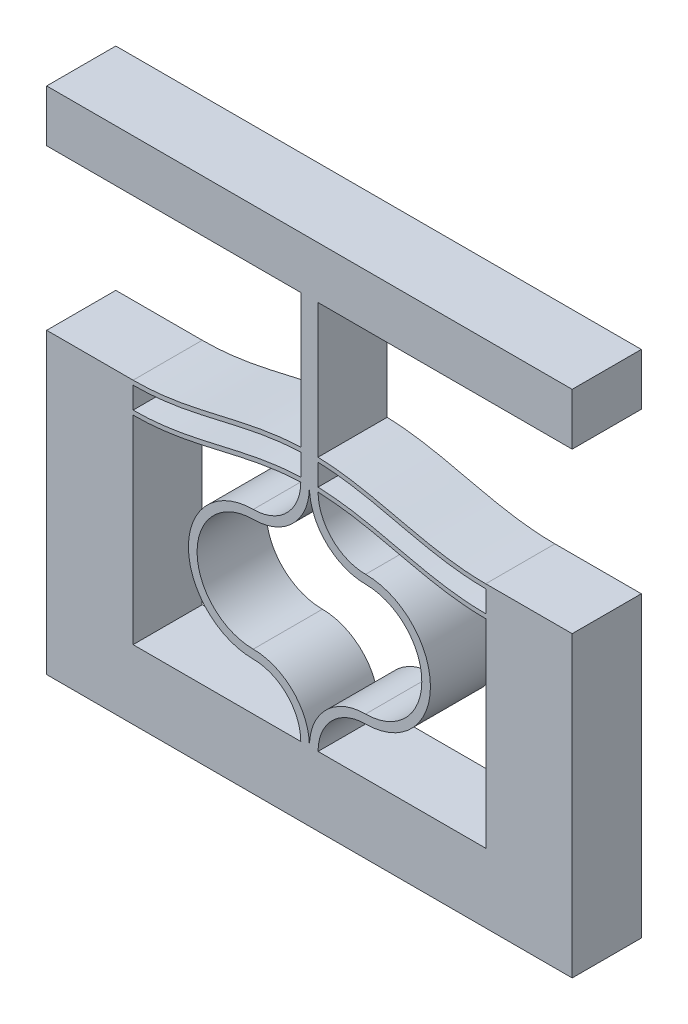
SolidWorks part; units mm, degrees
ref_plane "Front Plane" through (0, 0, 0) normal (0, 0, 1) x (1, 0, 0)
ref_plane "Top Plane" through (0, 0, 0) normal (0, 1, 0) x (1, 0, 0)
ref_plane "Right Plane" through (0, 0, 0) normal (1, 0, 0) x (0, 0, -1)
sketch "Sketch1" plane through (0, 0, 0) normal (0, 0, 1) x (1, 0, 0)
  line L4 (0, 11.5) -> (0, 0)
  line L5 (10.2, 0) -> (10.2, 13) construction
  line L6 (10.2, 13) -> (10.2, 15.9911) construction
  line L17 (9.7, 0) -> (0, 0)
  line L18 (10.7, 0) -> (20.4, 0)
  line L19 (20.4, 0) -> (20.4, 11.5)
  line L20 (10.7, 13.2411) -> (10.7, 14.4911)
  line L21 (9.7, 13.2411) -> (9.7, 14.4911)
  line L22 (10.7, 14.7411) -> (10.7, 15.9911)
  line L23 (10.7, 15.9911) -> (9.7, 15.9911)
  line L24 (9.7, 15.9911) -> (9.7, 14.7411)
  line L31 (-5, 13.25) -> (-5, -4)
  line L32 (-5, -4) -> (25.4, -4)
  line L33 (25.4, -4) -> (25.4, 13.25)
  line L34 (0, 11.75) -> (0, 13)
  line L36 (-5, 13.25) -> (0, 13.25)
  line L37 (25.4, 13.25) -> (20.4, 13.25)
  line L38 (20.4, 11.75) -> (20.4, 13)
  arc A0 (10.2, 13) -> (6.95, 9.75) centre (6.95, 13) cw
  arc A1 (6.95, 9.75) -> (6.95, 3.25) centre (6.95, 6.5) ccw
  arc A2 (6.95, 3.25) -> (10.2, 0) centre (6.95, 0) cw
  arc A3 (9.7, 12.9911) -> (6.95, 10.25) centre (6.95, 13) cw
  arc A4 (6.95, 10.25) -> (6.95, 2.75) centre (6.95, 6.5) ccw
  arc A5 (6.95, 2.75) -> (9.7, 0) centre (6.95, 0) cw
  arc A6 (9.7, 13) -> (6.95, 10.25) centre (6.95, 13) cw construction
  arc A7 (13.45, 3.25) -> (10.2, 0) centre (13.45, 0) ccw
  arc A8 (13.45, 2.75) -> (10.7, 0) centre (13.45, 0) ccw
  arc A9 (13.45, 9.75) -> (13.45, 3.25) centre (13.45, 6.5) cw
  arc A10 (13.45, 10.25) -> (13.45, 2.75) centre (13.45, 6.5) cw
  arc A11 (10.7, 12.9911) -> (13.45, 10.25) centre (13.45, 13) ccw
  arc A12 (10.2, 13) -> (13.45, 9.75) centre (13.45, 13) ccw
  spline S0 degree 4 poles (-2.0401, 11.8932) (-1.9772, 11.8846) (-1.8455, 11.8679) (-1.6624, 11.8447) (-1.3945, 11.8179) (-1.0936, 11.7897) (-0.7437, 11.7688) (-0.4752, 11.7554) (-0.0408, 11.749) (0.1102, 11.7499) (0.4738, 11.7558) (0.7092, 11.7679) (1.0334, 11.7851) (1.3516, 11.8128) (1.7502, 11.854) (2.1923, 11.9124) (2.7058, 11.9922) (3.3058, 12.1029) (4.0022, 12.2485) (4.9166, 12.4561) (5.9838, 12.707) (7.055, 12.9379) (8.1373, 13.1142) (9.0337, 13.2105) (9.8109, 13.2536) (10.5891, 13.2536) (11.3663, 13.2105) (12.2627, 13.1142) (13.3449, 12.9379) (14.4163, 12.707) (15.4832, 12.4561) (16.3198, 12.2662) (16.8578, 12.1523) (17.3629, 12.0533) (17.7764, 11.9798) (18.2035, 11.9124) (18.6563, 11.854) (18.9878, 11.8179) (19.2899, 11.793) (19.5137, 11.7765) (19.7423, 11.7659) (19.9174, 11.7558) (20.2941, 11.7499) (20.4363, 11.749) (20.8074, 11.7542) (21.0192, 11.7634) (21.2671, 11.7754) (21.4449, 11.7884) (21.6432, 11.8037) (21.8311, 11.8212) (22.0262, 11.8414) (22.2161, 11.864) (22.3445, 11.8804) (22.4082, 11.8889) (22.4399, 11.8932) knots 0 0 0 0 0 0.010394 0.020788 0.031182 0.041576 0.062112 0.07238 0.082649 0.098356 0.106209 0.114063 0.12977 0.145477 0.161184 0.176891 0.202819 0.228747 0.260161 0.291575 0.354403 0.405758 0.437172 0.468586 0.5 0.531414 0.562828 0.594242 0.645597 0.708425 0.739839 0.771253 0.784217 0.797181 0.823109 0.838816 0.854523 0.87023 0.878084 0.885937 0.893791 0.901644 0.917351 0.92762 0.937888 0.948156 0.958424 0.963621 0.968818 0.979212 0.989606 0.994803 1 1 1 1 1 construction
  spline S1 degree 4 poles (0, 11.75) (0.0812, 11.75) (0.1997, 11.7513) (0.4738, 11.7558) (0.7092, 11.7679) (1.0334, 11.7851) (1.3516, 11.8128) (1.7502, 11.854) (2.1923, 11.9124) (2.7058, 11.9922) (3.3058, 12.1029) (4.0022, 12.2485) (4.9166, 12.4561) (5.9838, 12.707) (7.055, 12.9379) (8.1373, 13.1142) (9.0337, 13.2105) (9.8109, 13.2536) (10.5891, 13.2536) (11.3663, 13.2105) (12.2627, 13.1142) (13.3449, 12.9379) (14.4163, 12.707) (15.4832, 12.4561) (16.3198, 12.2662) (16.8578, 12.1523) (17.3629, 12.0533) (17.7764, 11.9798) (18.2035, 11.9124) (18.6563, 11.854) (18.9878, 11.8179) (19.2899, 11.793) (19.5137, 11.7765) (19.7423, 11.7659) (19.9174, 11.7558) (20.2013, 11.7513) (20.3188, 11.75) (20.4, 11.75) knots 0.082649 0.082649 0.082649 0.082649 0.082649 0.098356 0.106209 0.114063 0.12977 0.145477 0.161184 0.176891 0.202819 0.228747 0.260161 0.291575 0.354403 0.405758 0.437172 0.468586 0.5 0.531414 0.562828 0.594242 0.645597 0.708425 0.739839 0.771253 0.784217 0.797181 0.823109 0.838816 0.854523 0.87023 0.878084 0.885937 0.893791 0.901644 0.917351 0.917351 0.917351 0.917351 0.917351
  spline S2 degree 4 poles (-2.0401, 13.1432) (-1.9772, 13.1346) (-1.8455, 13.1179) (-1.6624, 13.0947) (-1.3945, 13.0679) (-1.0936, 13.0397) (-0.7437, 13.0188) (-0.4752, 13.0054) (-0.0408, 12.999) (0.1102, 12.9999) (0.4738, 13.0058) (0.7092, 13.0179) (1.0334, 13.0351) (1.3516, 13.0628) (1.7502, 13.104) (2.1923, 13.1624) (2.7058, 13.2422) (3.3058, 13.3529) (4.0022, 13.4985) (4.9166, 13.7061) (5.9838, 13.957) (7.055, 14.1879) (8.1373, 14.3642) (9.0337, 14.4605) (9.8109, 14.5036) (10.5891, 14.5036) (11.3663, 14.4605) (12.2627, 14.3642) (13.3449, 14.1879) (14.4163, 13.957) (15.4832, 13.7061) (16.3198, 13.5162) (16.8578, 13.4023) (17.3629, 13.3033) (17.7764, 13.2298) (18.2035, 13.1624) (18.6563, 13.104) (18.9878, 13.0679) (19.2899, 13.043) (19.5137, 13.0265) (19.7423, 13.0159) (19.9174, 13.0058) (20.2941, 12.9999) (20.4363, 12.999) (20.8074, 13.0042) (21.0192, 13.0134) (21.2671, 13.0254) (21.4449, 13.0384) (21.6432, 13.0537) (21.8311, 13.0712) (22.0262, 13.0914) (22.2161, 13.114) (22.3445, 13.1304) (22.4082, 13.1389) (22.4399, 13.1432) knots 0 0 0 0 0 0.010394 0.020788 0.031182 0.041576 0.062112 0.07238 0.082649 0.098356 0.106209 0.114063 0.12977 0.145477 0.161184 0.176891 0.202819 0.228747 0.260161 0.291575 0.354403 0.405758 0.437172 0.468586 0.5 0.531414 0.562828 0.594242 0.645597 0.708425 0.739839 0.771253 0.784217 0.797181 0.823109 0.838816 0.854523 0.87023 0.878084 0.885937 0.893791 0.901644 0.917351 0.92762 0.937888 0.948156 0.958424 0.963621 0.968818 0.979212 0.989606 0.994803 1 1 1 1 1 construction
  spline S3 degree 4 poles (0, 13) (0.0812, 13) (0.1997, 13.0013) (0.4738, 13.0058) (0.7092, 13.0179) (1.0334, 13.0351) (1.3516, 13.0628) (1.7502, 13.104) (2.1923, 13.1624) (2.7058, 13.2422) (3.3058, 13.3529) (4.0022, 13.4985) (4.9166, 13.7061) (5.9838, 13.957) (7.055, 14.1879) (8.1373, 14.3642) (9.0337, 14.4605) (9.8109, 14.5036) (10.5891, 14.5036) (11.3663, 14.4605) (12.2627, 14.3642) (13.3449, 14.1879) (14.4163, 13.957) (15.4832, 13.7061) (16.3198, 13.5162) (16.8578, 13.4023) (17.3629, 13.3033) (17.7764, 13.2298) (18.2035, 13.1624) (18.6563, 13.104) (18.9878, 13.0679) (19.2899, 13.043) (19.5137, 13.0265) (19.7423, 13.0159) (19.9174, 13.0058) (20.2013, 13.0013) (20.3188, 13) (20.4, 13) knots 0.082649 0.082649 0.082649 0.082649 0.082649 0.098356 0.106209 0.114063 0.12977 0.145477 0.161184 0.176891 0.202819 0.228747 0.260161 0.291575 0.354403 0.405758 0.437172 0.468586 0.5 0.531414 0.562828 0.594242 0.645597 0.708425 0.739839 0.771253 0.784217 0.797181 0.823109 0.838816 0.854523 0.87023 0.878084 0.885937 0.893791 0.901644 0.917351 0.917351 0.917351 0.917351 0.917351
  spline S4 degree 4 poles (-2.0401, 13.3932) (-1.9772, 13.3846) (-1.8455, 13.3679) (-1.6624, 13.3447) (-1.3945, 13.3179) (-1.0936, 13.2897) (-0.7437, 13.2688) (-0.4752, 13.2554) (-0.0408, 13.249) (0.1102, 13.2499) (0.4738, 13.2558) (0.7092, 13.2679) (1.0334, 13.2851) (1.3516, 13.3128) (1.7502, 13.354) (2.1923, 13.4124) (2.7058, 13.4922) (3.3058, 13.6029) (4.0022, 13.7485) (4.9166, 13.9561) (5.9838, 14.207) (7.055, 14.4379) (8.1373, 14.6142) (9.0337, 14.7105) (9.8109, 14.7536) (10.5891, 14.7536) (11.3663, 14.7105) (12.2627, 14.6142) (13.3449, 14.4379) (14.4163, 14.207) (15.4832, 13.9561) (16.3198, 13.7662) (16.8578, 13.6523) (17.3629, 13.5533) (17.7764, 13.4798) (18.2035, 13.4124) (18.6563, 13.354) (18.9878, 13.3179) (19.2899, 13.293) (19.5137, 13.2765) (19.7423, 13.2659) (19.9174, 13.2558) (20.2941, 13.2499) (20.4363, 13.249) (20.8074, 13.2542) (21.0192, 13.2634) (21.2671, 13.2754) (21.4449, 13.2884) (21.6432, 13.3037) (21.8311, 13.3212) (22.0262, 13.3414) (22.2161, 13.364) (22.3445, 13.3804) (22.4082, 13.3889) (22.4399, 13.3932) knots 0 0 0 0 0 0.010394 0.020788 0.031182 0.041576 0.062112 0.07238 0.082649 0.098356 0.106209 0.114063 0.12977 0.145477 0.161184 0.176891 0.202819 0.228747 0.260161 0.291575 0.354403 0.405758 0.437172 0.468586 0.5 0.531414 0.562828 0.594242 0.645597 0.708425 0.739839 0.771253 0.784217 0.797181 0.823109 0.838816 0.854523 0.87023 0.878084 0.885937 0.893791 0.901644 0.917351 0.92762 0.937888 0.948156 0.958424 0.963621 0.968818 0.979212 0.989606 0.994803 1 1 1 1 1 construction
  spline S5 degree 4 poles (0, 13.25) (0.0812, 13.25) (0.1997, 13.2513) (0.4738, 13.2558) (0.7092, 13.2679) (1.0334, 13.2851) (1.3516, 13.3128) (1.7502, 13.354) (2.1923, 13.4124) (2.7058, 13.4922) (3.3058, 13.6029) (4.0022, 13.7485) (4.9166, 13.9561) (5.9838, 14.207) (7.055, 14.4379) (8.1373, 14.6142) (9.0337, 14.7105) (9.8109, 14.7536) (10.5891, 14.7536) (11.3663, 14.7105) (12.2627, 14.6142) (13.3449, 14.4379) (14.4163, 14.207) (15.4832, 13.9561) (16.3198, 13.7662) (16.8578, 13.6523) (17.3629, 13.5533) (17.7764, 13.4798) (18.2035, 13.4124) (18.6563, 13.354) (18.9878, 13.3179) (19.2899, 13.293) (19.5137, 13.2765) (19.7423, 13.2659) (19.9174, 13.2558) (20.2013, 13.2513) (20.3188, 13.25) (20.4, 13.25) knots 0.082649 0.082649 0.082649 0.082649 0.082649 0.098356 0.106209 0.114063 0.12977 0.145477 0.161184 0.176891 0.202819 0.228747 0.260161 0.291575 0.354403 0.405758 0.437172 0.468586 0.5 0.531414 0.562828 0.594242 0.645597 0.708425 0.739839 0.771253 0.784217 0.797181 0.823109 0.838816 0.854523 0.87023 0.878084 0.885937 0.893791 0.901644 0.917351 0.917351 0.917351 0.917351 0.917351
  spline S8 degree 4 poles (-2.0401, 11.6432) (-1.9772, 11.6346) (-1.8455, 11.6179) (-1.6624, 11.5947) (-1.3945, 11.5679) (-1.0936, 11.5397) (-0.7437, 11.5188) (-0.4752, 11.5054) (-0.0408, 11.499) (0.1102, 11.4999) (0.4738, 11.5058) (0.7092, 11.5179) (1.0334, 11.5351) (1.3516, 11.5628) (1.7502, 11.604) (2.1923, 11.6624) (2.7058, 11.7422) (3.3058, 11.8529) (4.0022, 11.9985) (4.9166, 12.2061) (5.9838, 12.457) (7.055, 12.6879) (8.1373, 12.8642) (9.0337, 12.9605) (9.8109, 13.0036) (10.5891, 13.0036) (11.3663, 12.9605) (12.2627, 12.8642) (13.3449, 12.6879) (14.4163, 12.457) (15.4832, 12.2061) (16.3198, 12.0162) (16.8578, 11.9023) (17.3629, 11.8033) (17.7764, 11.7298) (18.2035, 11.6624) (18.6563, 11.604) (18.9878, 11.5679) (19.2899, 11.543) (19.5137, 11.5265) (19.7423, 11.5159) (19.9174, 11.5058) (20.2941, 11.4999) (20.4363, 11.499) (20.8074, 11.5042) (21.0192, 11.5134) (21.2671, 11.5254) (21.4449, 11.5384) (21.6432, 11.5537) (21.8311, 11.5712) (22.0262, 11.5914) (22.2161, 11.614) (22.3445, 11.6304) (22.4082, 11.6389) (22.4399, 11.6432) knots 0 0 0 0 0 0.010394 0.020788 0.031182 0.041576 0.062112 0.07238 0.082649 0.098356 0.106209 0.114063 0.12977 0.145477 0.161184 0.176891 0.202819 0.228747 0.260161 0.291575 0.354403 0.405758 0.437172 0.468586 0.5 0.531414 0.562828 0.594242 0.645597 0.708425 0.739839 0.771253 0.784217 0.797181 0.823109 0.838816 0.854523 0.87023 0.878084 0.885937 0.893791 0.901644 0.917351 0.92762 0.937888 0.948156 0.958424 0.963621 0.968818 0.979212 0.989606 0.994803 1 1 1 1 1 construction
  spline S9 degree 4 poles (0, 11.5) (0.0812, 11.5) (0.1997, 11.5013) (0.4738, 11.5058) (0.7092, 11.5179) (1.0334, 11.5351) (1.3516, 11.5628) (1.7502, 11.604) (2.1923, 11.6624) (2.7058, 11.7422) (3.3058, 11.8529) (4.0022, 11.9985) (4.9166, 12.2061) (5.9838, 12.457) (7.055, 12.6879) (8.1373, 12.8642) (9.0337, 12.9605) (9.8109, 13.0036) (10.5891, 13.0036) (11.3663, 12.9605) (12.2627, 12.8642) (13.3449, 12.6879) (14.4163, 12.457) (15.4832, 12.2061) (16.3198, 12.0162) (16.8578, 11.9023) (17.3629, 11.8033) (17.7764, 11.7298) (18.2035, 11.6624) (18.6563, 11.604) (18.9878, 11.5679) (19.2899, 11.543) (19.5137, 11.5265) (19.7423, 11.5159) (19.9174, 11.5058) (20.2013, 11.5013) (20.3188, 11.5) (20.4, 11.5) knots 0.082649 0.082649 0.082649 0.082649 0.082649 0.098356 0.106209 0.114063 0.12977 0.145477 0.161184 0.176891 0.202819 0.228747 0.260161 0.291575 0.354403 0.405758 0.437172 0.468586 0.5 0.531414 0.562828 0.594242 0.645597 0.708425 0.739839 0.771253 0.784217 0.797181 0.823109 0.838816 0.854523 0.87023 0.878084 0.885937 0.893791 0.901644 0.917351 0.917351 0.917351 0.917351 0.917351
  dimension "D4" = 0.25
  dimension "D6" = 4
  dimension "D1" = 13
  dimension "D2" = 0.5
  dimension "D3" = 0.25
  dimension "D7" = 5
  dimension "D5" = 1.5
extrude "Boss-Extrude1" add sketch "Sketch1" along normal blind 4
sketch "Sketch4" plane through (0, 15.9911, 0) normal (0, 1, 0) x (1, 0, 0)
  line L24 (10.7, 0) -> (9.7, 0)
  line L25 (9.7, 0) -> (9.7, -4)
  line L26 (10.7, 0) -> (9.7, 0)
  line L27 (10.7, -4) -> (10.7, 0)
  line L29 (9.7, 0) -> (9.7, -4)
  line L31 (10.7, -4) -> (10.7, 0)
  line L32 (9.7, -4) -> (10.7, -4)
  line L33 (9.7, -4) -> (10.7, -4)
  dimension "D1" = 0
extrude "Boss-Extrude2" add sketch "Sketch4" along normal blind 1.5
mirror "Mirror3" [suppressed]
ref_plane "Plane1" [suppressed] through (10.2, 0, 0) normal (-1, 0, 0) x (0, 0, 1)
split "Split2" [suppressed] bodies to split 247 102
sketch "Sketch7" [suppressed] plane through (10.2, 0, 0) normal (-1, 0, 0) x (0, 0, 1)
  line L4 (4, 34.9822) -> (4, 38.9822)
  line L12 (0, 13) -> (4, 13)
  line L13 (0, 13) -> (4, 13)
  line L14 (4, 13) -> (4, 21.9822)
  line L15 (4, 13) -> (4, 21.9822)
  line L20 (4, 0) -> (0, 0)
  line L22 (4, 0) -> (0, 0)
  line L23 (0, -4) -> (4, -4)
  line L27 (0, -4) -> (4, -4)
  line L31 (4, 21.9822) -> (0, 21.9822)
  line L32 (4, 21.9822) -> (0, 21.9822)
  line L33 (0, 21.9822) -> (0, 13)
  line L34 (0, 21.9822) -> (0, 13)
  line L36 (4, -4) -> (4, 0)
  line L38 (4, 34.9822) -> (4, 38.9822)
  line L39 (4, 34.9822) -> (4, 38.9822)
  line L40 (4, 38.9822) -> (0, 38.9822)
  line L41 (4, 38.9822) -> (0, 38.9822)
  line L46 (4, 34.9822) -> (4, 38.9822)
  line L51 (0, 38.9822) -> (0, 34.9822)
  line L52 (0, 38.9822) -> (0, 34.9822)
  line L53 (0, 34.9822) -> (4, 34.9822)
  line L54 (0, 34.9822) -> (4, 34.9822)
  line L55 (4, 38.9822) -> (0, 38.9822)
  line L57 (4, 38.9822) -> (0, 38.9822)
  line L59 (4, -4) -> (4, 0)
  line L60 (0, 0) -> (0, -4)
  line L61 (0, 0) -> (0, -4)
  line L62 (0, 38.9822) -> (0, 34.9822)
  line L63 (0, 38.9822) -> (0, 34.9822)
  line L64 (0, 34.9822) -> (4, 34.9822)
  line L65 (0, 34.9822) -> (4, 34.9822)
  dimension "D1" = 0
  dimension "D2" = 0
  dimension "D3" = 0
  dimension "D4" = 0
extrude "Boss-Extrude3" [suppressed] add sketch "Sketch7" along normal blind 4
mirror "Mirror2" [suppressed]
other "Move Face1" face at (10.2, 17.4911, 2) parameters "D1"=5
sketch "Sketch8" plane through (0, 0, 4) normal (0, 0, 1) x (1, 0, 0)
  line L0 (-5, 13.25) -> (-5, -4) construction
  line L1 (-5, 25.4911) -> (25.4, 25.4911)
  line L2 (-5, 25.4911) -> (-5, 22.4911)
  line L3 (-5, 22.4911) -> (25.4, 22.4911)
  line L4 (25.4, 25.4911) -> (25.4, 22.4911)
  line L5 (25.4, -4) -> (25.4, 13.25) construction
  dimension "D1" = 3
extrude "Boss-Extrude4" add sketch "Sketch8" against normal up to surface (4 mm away) up to face at (13.125, 13.4933, 0)
